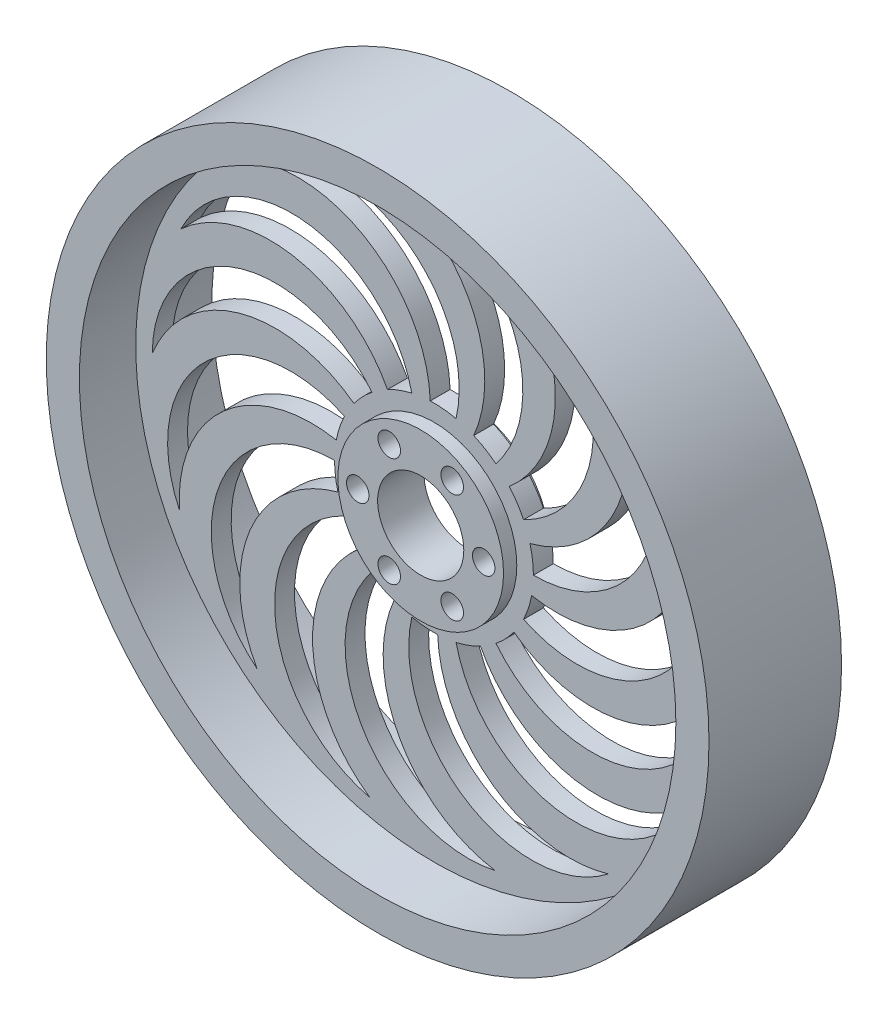
SolidWorks part; units mm, degrees
ref_plane "Front Plane" through (0, 0, 0) normal (0, 0, 1) x (1, 0, 0)
ref_plane "Top Plane" through (0, 0, 0) normal (0, 1, 0) x (1, 0, 0)
ref_plane "Right Plane" through (0, 0, 0) normal (1, 0, 0) x (0, 0, -1)
sketch "Sketch1" plane through (0, 0, 0) normal (0, 1, 0) x (1, 0, 0)
  line L0 (0, -77.7422) -> (0, 81.729) construction
  line L1 (9.5, 19.6041) -> (9.5, -23.4618) construction
  line L2 (6.5, -3.5) -> (12.5, -3.5)
  line L3 (6.5, -3.5) -> (6.5, 3.5)
  line L4 (6.5, 3.5) -> (12.5, 3.5)
  line L5 (12.5, -3.5) -> (12.5, 3.5)
  line L6 (6.5, -3.5) -> (12.5, 3.5) construction
  line L7 (6.5, 3.5) -> (12.5, -3.5) construction
  line L8 (45, -1.5) -> (12.5, -1.5)
  line L9 (45, -1.5) -> (45, 1.5)
  line L10 (45, 1.5) -> (12.5, 1.5)
  line L11 (12.5, -1.5) -> (12.5, 1.5)
  line L12 (45, -1.5) -> (12.5, 1.5) construction
  line L13 (45, 1.5) -> (12.5, -1.5) construction
  line L14 (50, -10) -> (45, -10)
  line L15 (50, -10) -> (50, 10)
  line L16 (50, 10) -> (45, 10)
  line L17 (45, -10) -> (45, 10)
  line L18 (50, -10) -> (45, 10) construction
  line L19 (50, 10) -> (45, -10) construction
  point P2 (9.5, 0)
  point P8 (28.75, 0)
  point P13 (47.5, 0)
  dimension "D1" = 6
  dimension "D3" = 5
  dimension "D4" = 100
  dimension "D5" = 7
  dimension "D6" = 3
  dimension "D7" = 20
  dimension "D8" = 9.5
revolve "Revolve1" add sketch "Sketch1" angle 360 about L0
sketch "Sketch2" plane through (0, 0, 3.5) normal (0, 0, 1) x (1, 0, 0)
  line L0 (0, 0) -> (12.5, 0) construction
  circle A0 centre (0, 0) radius 12.5 construction
  point P6 (9.5, 0)
  point P7 (4.75, -8.2272)
  point P10 (-4.75, -8.2272)
  point P11 (-9.5, 0)
  point P12 (-4.75, 8.2272)
  point P13 (4.75, 8.2272)
  point P14 (0, 0)
  dimension "D1" = 9.5
  dimension "D2" = 6
hole_wizard "M3 Clearance Hole1" positions "Sketch3" profile "Sketch4" hole size "M3" standard "ANSI Metric" end condition through all
sketch "Sketch3" plane through (0, 0, 3.5) normal (0, 0, 1) x (1, 0, 0)
  point P0 (-4.75, 8.2272)
  point P3 (4.75, 8.2272)
  point P6 (9.5, 0)
  point P9 (4.75, -8.2272)
  point P12 (-4.75, -8.2272)
  point P15 (-9.5, 0)
sketch "Sketch4" plane through (-4.75, 8.2272, 3.5) normal (1, 0, 0) x (0, -1, 0)
  line L0 (0, 0) -> (0, 13.5)
  line L1 (0, 13.5) -> (1.7, 13.5)
  line L2 (1.7, 13.5) -> (1.7, 0)
  line L5 (1.7, 0) -> (0, 0)
  line L11 (0, -6.35) -> (0, 107.95) construction
  dimension "Thru Hole Dia." = 3.4
  dimension "Thru Hole Depth" = 13.5
sketch "Sketch5" plane through (0, 0, 1.5) normal (0, 0, 1) x (1, 0, 0)
  line L0 (0, 0) -> (45, 0) construction
  line L1 (0, 0) -> (43.4667, 11.6469) construction
  circle A0 centre (0, 0) radius 45 construction
  circle A1 centre (0, 0) radius 15
  circle A2 centre (0, 0) radius 12.5 construction
  circle A3 centre (0, 0) radius 42.5
  arc A4 (15, 0) -> (26.6769, 33.0846) centre (15, 18.6029) ccw
  circle A5 centre (0, 0) radius 45 construction
  arc A6 (14.4889, 3.8823) -> (26.6769, 33.0846) centre (9.3166, 23.1856) ccw
  dimension "D1" = 2.5
  dimension "D2" = 2.5
  dimension "D3" = 15
extrude "Cut-Extrude1" cut sketch "Sketch5" against normal through all contours A6 A1 A4
pattern_circular "CirPattern1" count 14 over 360 about axis through (0, 0, 0) along (0, 0, 1) of "Cut-Extrude1"
